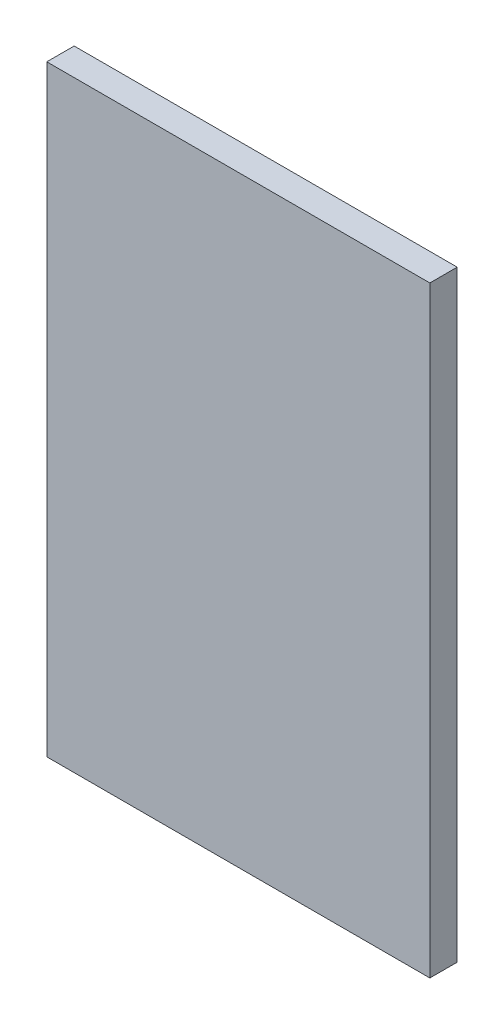
SolidWorks part; units mm, degrees
ref_plane "Front Plane" through (0, 0, 0) normal (0, 0, 1) x (1, 0, 0)
ref_plane "Top Plane" through (0, 0, 0) normal (0, 1, 0) x (1, 0, 0)
ref_plane "Right Plane" through (0, 0, 0) normal (1, 0, 0) x (0, 0, -1)
sketch "Sketch2" plane through (0, 0, 0) normal (0, 0, 1) x (1, 0, 0)
  line L1 (-177.8, 279.4) -> (177.8, 279.4)
  line L2 (-177.8, 279.4) -> (-177.8, -279.4)
  line L3 (-177.8, -279.4) -> (177.8, -279.4)
  line L4 (177.8, 279.4) -> (177.8, -279.4)
  point P4 (0, 279.4)
  point P6 (177.8, 0)
  dimension "D1" = 355.6
  dimension "D2" = 558.8
  dimension "D3" = 0
  dimension "D4" = 0
extrude "Boss-Extrude1" add sketch "Sketch2" along normal blind 25.4
sketch "Sketch3" plane through (0, 0, 25.4) normal (0, 0, 1) x (1, 0, 0)
  line L0 (177.8, 279.4) -> (-177.8, 279.4) construction
  line L1 (-177.8, 279.4) -> (-177.8, -279.4) construction
  circle A0 centre (-171.45, 273.05) radius 4.7625
  dimension "D1" = 9.525
  dimension "D2" = 6.35
  dimension "D3" = 6.35
